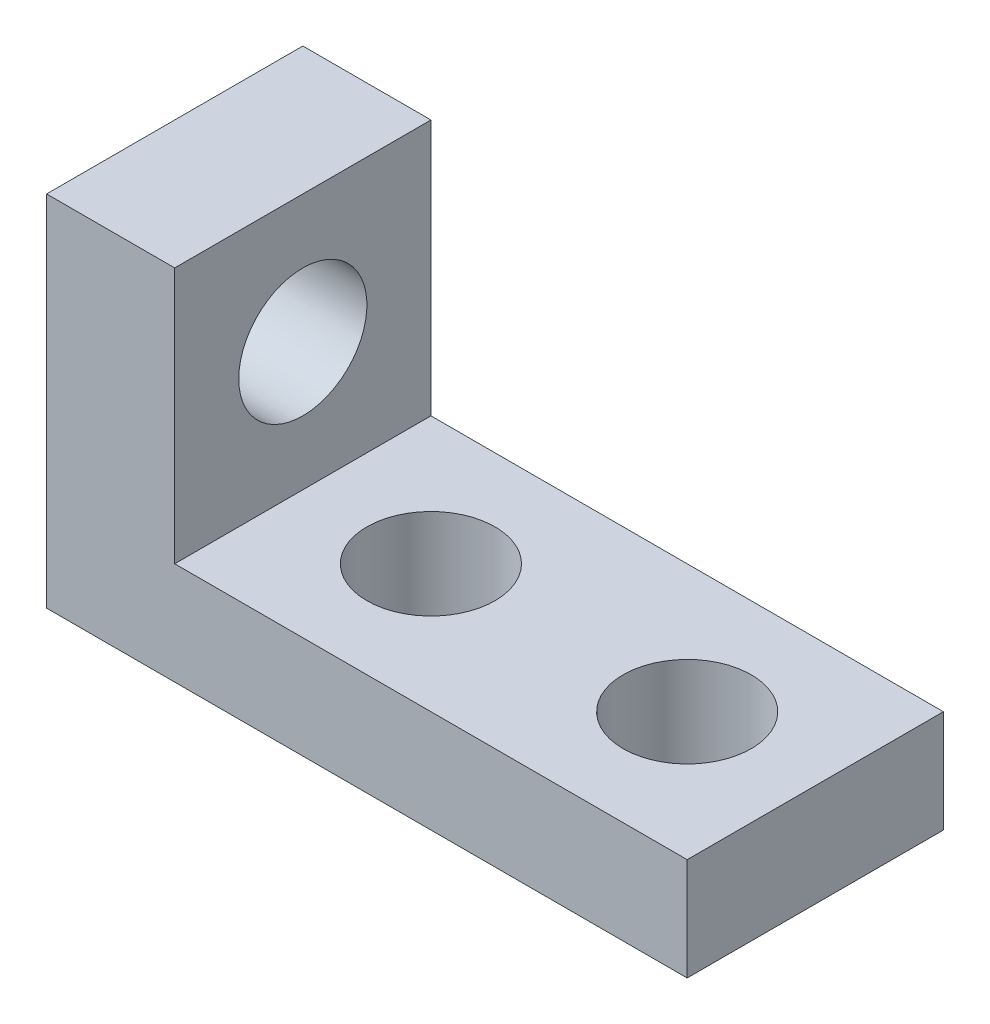
SolidWorks part; units mm, degrees
ref_plane "Front Plane" through (0, 0, 0) normal (0, 0, 1) x (1, 0, 0)
ref_plane "Top Plane" through (0, 0, 0) normal (0, 1, 0) x (1, 0, 0)
ref_plane "Right Plane" through (0, 0, 0) normal (1, 0, 0) x (0, 0, -1)
sketch "Sketch1" plane through (0, 0, 0) normal (0, 1, 0) x (1, 0, 0)
  line L0 (-9.525, 3.175) -> (-3.175, 3.175) construction
  line L1 (0, 0) -> (-12.7, 0)
  line L2 (0, 0) -> (0, 6.35)
  line L3 (0, 6.35) -> (-12.7, 6.35)
  line L4 (-12.7, 0) -> (-12.7, 6.35)
  circle A0 centre (-3.175, 3.175) radius 1.5875
  circle A1 centre (-9.525, 3.175) radius 1.5875
  point P5 (0, 0)
  point P9 (0, 0)
  point P10 (0, 3.175)
  point P11 (-6.35, 3.175)
  point P14 (-6.35, 6.35)
  dimension "D1" = 3.175
  dimension "D2" = 6.35
  dimension "D3" = 12.7
  dimension "D4" = 6.35
extrude "Boss-Extrude1" add sketch "Sketch1" along normal blind 2.54
sketch "Sketch2" plane through (-12.7, 0, 0) normal (-1, 0, 0) x (0, 0, 1)
  line L0 (-6.35, 2.54) -> (0, 2.54) construction
  line L1 (0, 2.54) -> (0, 0) construction
  line L2 (-6.35, 0) -> (0, 0)
  line L3 (-6.35, 0) -> (-6.35, 8.89)
  line L4 (-6.35, 8.89) -> (0, 8.89)
  line L5 (0, 0) -> (0, 8.89)
  circle A0 centre (-3.175, 5.715) radius 1.5875
  point P5 (-3.175, 2.54)
  dimension "D1" = 3.175
  dimension "D2" = 3.175
  dimension "D3" = 3.175
extrude "Boss-Extrude2" add sketch "Sketch2" along normal blind 3.175
